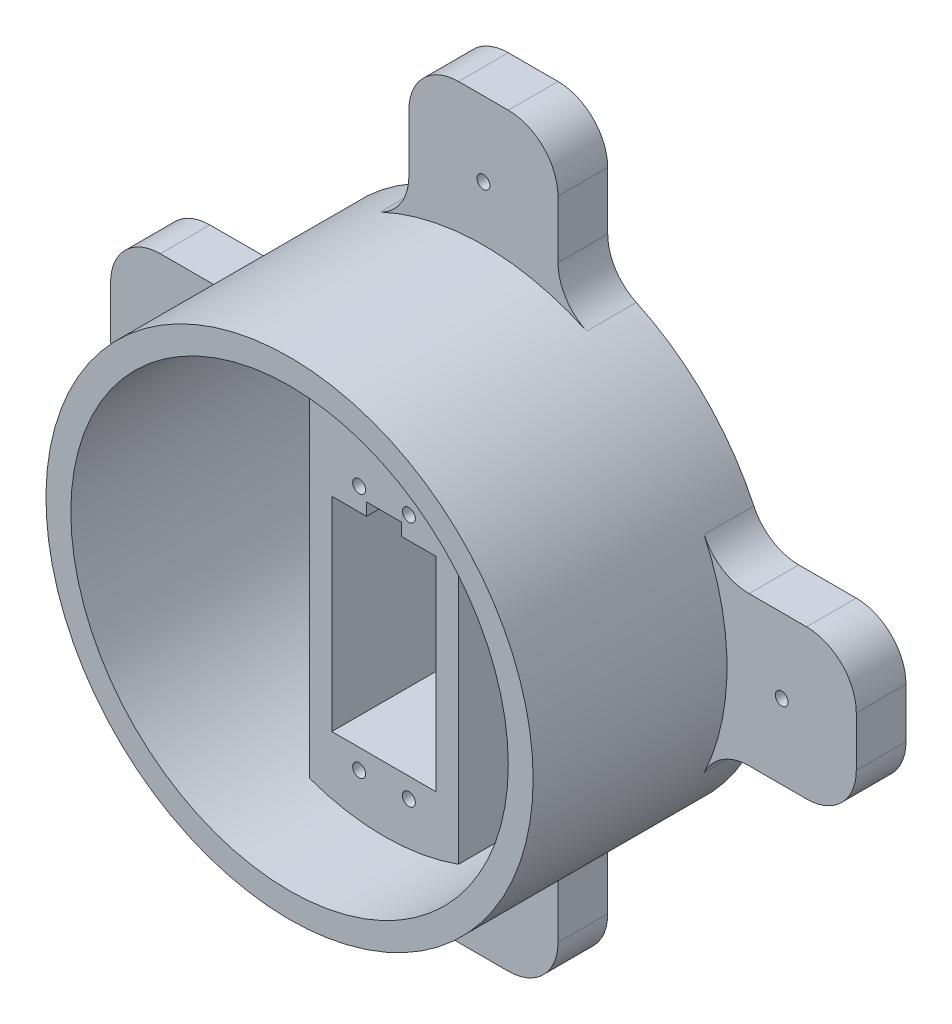
SolidWorks part; units mm, degrees
material "PLA"
ref_plane "Blat stołu" through (0, 0, 0) normal (0, 0, 1) x (1, 0, 0)
ref_plane "Płaszczyzna górna" through (0, 0, 0) normal (0, 1, 0) x (1, 0, 0)
ref_plane "Płaszczyzna prawa" through (0, 0, 0) normal (1, 0, 0) x (0, 0, -1)
sketch "Szkic1" plane through (0, 0, 0) normal (0, 0, 1) x (1, 0, 0)
  circle A0 centre (0, 0) radius 49
  circle A1 centre (0, 0) radius 44
  dimension "D1" = 98
  dimension "D2" = 88
extrude "Dodanie-wyciągnięcie1" add sketch "Szkic1" along normal blind 49
sketch "Szkic2" plane through (0, 0, 0) normal (0, 0, 1) x (1, 0, 0)
  line L0 (15, 46.6476) -> (15, -46.6476)
  line L1 (-15, 46.6476) -> (-15, -46.6476)
  circle A0 centre (0, 0) radius 49 construction
  circle A1 centre (0, 0) radius 49 construction
  arc A2 (15, -46.6476) -> (-15, -46.6476) centre (0, 0) cw
  arc A3 (15, 46.6476) -> (-15, 46.6476) centre (0, 0) ccw
  point P0 (15, 46.6476)
  point P1 (-15, 46.6476)
  point P4 (-15, -46.6476)
  point P5 (15, -46.6476)
  dimension "D1" = 30
extrude "Dodanie-wyciągnięcie2" add sketch "Szkic2" along normal blind 30
sketch "Szkic3" plane through (0, 0, 30) normal (0, 0, 1) x (1, 0, 0)
  line L0 (15, -41.3642) -> (15, 41.3642) construction
  line L6 (-10.5, -31) -> (10.5, -31)
  line L7 (-10.5, -31) -> (-10.5, 10)
  line L8 (-10.5, 10) -> (10.5, 10)
  line L9 (10.5, -31) -> (10.5, 10)
  line L10 (-10.5, -31) -> (10.5, 10) construction
  line L11 (-10.5, 10) -> (10.5, -31) construction
  point P0 (0, -10.5)
  dimension "D1" = 21
  dimension "D2" = 41
  dimension "D3" = 31
extrude "Wytnij-wyciągnięcie1" cut sketch "Szkic3" against normal blind 30
sketch "Szkic4" plane through (0, 0, 0) normal (0, 0, -1) x (-1, 0, 0)
  line L0 (-10.5, 10) -> (10.5, 10) construction
  point P0 (5, 14.5)
  point P1 (-5, 14.5)
  point P2 (-5, -35)
  point P3 (5, -35)
  dimension "D1" = 10
  dimension "D2" = 4.5
  dimension "D3" = 49.5
  dimension "D6" = 5
sketch "Szkic5" plane through (0, 0, 0) normal (0, 0, -1) x (-1, 0, 0)
  line L0 (10.5, -31) -> (-10.5, -31) construction
  line L1 (6.1547, -33) -> (3.8453, -33)
  line L2 (3.8453, -33) -> (2.6906, -35)
  line L3 (2.6906, -35) -> (3.8453, -37)
  line L4 (3.8453, -37) -> (6.1547, -37)
  line L5 (6.1547, -37) -> (7.3094, -35)
  line L6 (7.3094, -35) -> (6.1547, -33)
  circle A0 centre (5, -35) radius 2 construction
  dimension "D1" = 4
extrude "Wytnij-wyciągnięcie2" cut sketch "Szkic5" against normal blind 20
pattern_sketch "Szkic-szyk1" of "Wytnij-wyciągnięcie2" driven by "Szkic4"
hole_wizard "Otwór pod śrubę M21" positions "Szkic6" profile "Szkic7" hole size "M2" standard "ISO" end condition up to next
sketch "Szkic6" plane through (0, 0, 20) normal (0, 0, -1) x (-1, 0, 0)
  point P0 (-5, 14.5)
sketch "Szkic7" plane through (5, 14.5, 20) normal (1, 0, 0) x (0, 1, 0)
  line L0 (0, 0) -> (0, 10.001)
  line L1 (0, 10.001) -> (1.3, 10.001)
  line L2 (1.3, 10.001) -> (1.3, 0)
  line L5 (1.3, 0) -> (0, 0)
  line L11 (0, -6.35) -> (0, 107.95) construction
  dimension "Średnica otworu na wylot" = 2.6
  dimension "Głębokość otworu na wylot" = 10.001
pattern_sketch "Szkic-szyk2" of "Otwór pod śrubę M21" driven by "Szkic4"
sketch "Szkic8" plane through (0, 0, 30) normal (0, 0, 1) x (1, 0, 0)
  line L0 (10.5, 10) -> (-10.5, 10) construction
  line L1 (-3.5, 7.5) -> (3.5, 7.5)
  line L2 (-3.5, 7.5) -> (-3.5, 12.5)
  line L3 (-3.5, 12.5) -> (3.5, 12.5)
  line L4 (3.5, 7.5) -> (3.5, 12.5)
  line L5 (-3.5, 7.5) -> (3.5, 12.5) construction
  line L6 (-3.5, 12.5) -> (3.5, 7.5) construction
  point P0 (0, 10)
  dimension "D1" = 7
  dimension "D2" = 5
  dimension "D3" = 2.5
extrude "Wytnij-wyciągnięcie3" cut sketch "Szkic8" against normal up to next
sketch "Szkic9" plane through (0, 0, 0) normal (0, 0, -1) x (-1, 0, 0)
  line L5 (10.5, 10) -> (10.5, -31) construction
  line L7 (-75, -15) -> (-41.3642, -15)
  line L8 (-75, -15) -> (-75, 15)
  line L9 (-75, 15) -> (-41.3642, 15)
  circle A1 centre (0, 0) radius 49 construction
  arc A2 (-41.3642, -15) -> (-41.3642, 15) centre (0, 0) cw
  arc A3 (-15, 41.3642) -> (-15, -41.3642) centre (0, 0) ccw construction
  dimension "D1" = 30
  dimension "D2" = 85.5
extrude "Dodanie-wyciągnięcie3" add sketch "Szkic9" against normal blind 10 contours L9 A2 L7 L8
hole_wizard "Otwór pod śrubę M22" positions "Szkic10" profile "Szkic11" hole size "M2" standard "ISO" end condition through all
sketch "Szkic10" plane through (0, 0, 10) normal (0, 0, 1) x (1, 0, 0)
  line L0 (75, -15) -> (46.6476, -15) construction
  point P0 (60, 0)
  dimension "D1" = 15
  dimension "D2" = 15
sketch "Szkic11" plane through (60, 0, 10) normal (1, 0, 0) x (0, -1, 0)
  line L0 (0, 0) -> (0, 10)
  line L1 (0, 10) -> (1.3, 10)
  line L2 (1.3, 10) -> (1.3, 0)
  line L5 (1.3, 0) -> (0, 0)
  line L11 (0, -6.35) -> (0, 107.95) construction
  dimension "Średnica otworu na wylot" = 2.6
  dimension "Głębokość otworu na wylot" = 10
pattern_circular "Szyk kołowy1" count 4 every 90 about axis through (0, 0, 0) along (0, 0, 1) of "Dodanie-wyciągnięcie3", "Otwór pod śrubę M22"
fillet "Zaokrąglenie1" radius 10 16 edges at (-15, 46.6476, 5) (-15, 75, 5) (15, 75, 5) (15, 46.6476, 5) (46.6476, 15, 5) (75, 15, 5) (75, -15, 5) (46.6476, -15, 5) (15, -46.6476, 5) (15, -75, 5) (-15, -46.6476, 5) (-15, -75, 5) (-46.6476, -15, 5) (-46.6476, 15, 5) (-75, 15, 5) (-75, -15, 5)
